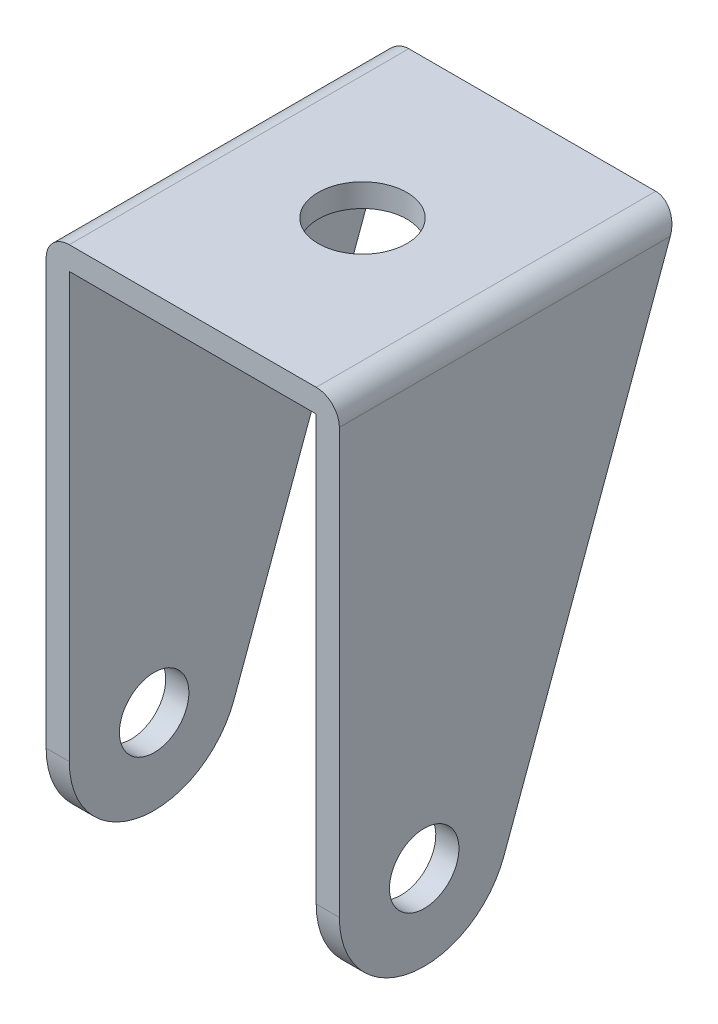
SolidWorks part; units mm, degrees
ref_plane "Front Plane" through (0, 0, 0) normal (0, 0, 1) x (1, 0, 0)
ref_plane "Top Plane" through (0, 0, 0) normal (0, 1, 0) x (1, 0, 0)
ref_plane "Right Plane" through (0, 0, 0) normal (1, 0, 0) x (0, 0, -1)
sketch "Sketch1" plane through (0, 0, 0) normal (1, 0, 0) x (0, 0, -1)
  line L0 (-11, 0) -> (-11, 58)
  line L1 (-11, 58) -> (33, 58)
  line L2 (33, 58) -> (10.3267, -3.7893)
  arc A0 (-11, 0) -> (10.3267, -3.7893) centre (0, 0) ccw
  dimension "D1" = 22
  dimension "D2" = 58
  dimension "D3" = 44
extrude "Boss-Extrude1" add sketch "Sketch1" along normal mid plane 38
sketch "Sketch2" plane through (0, 0, 11) normal (0, 0, 1) x (1, 0, 0)
  line L0 (-19, 58) -> (-19, 0) construction
  line L1 (-19, 58) -> (-19, 0)
  line L2 (19, 58) -> (-19, 58) construction
  line L3 (19, 58) -> (-19, 58)
  line L4 (19, 58) -> (19, 0) construction
  line L5 (19, 58) -> (19, 0)
  line L7 (19, -11) -> (19, 0) construction
  line L9 (19, -11) -> (19, 0)
  line L10 (-19, 0) -> (-19, -11) construction
  line L11 (-19, 0) -> (-19, -11)
  line L12 (16, -11) -> (16, 0)
  line L13 (16, 55) -> (16, 0)
  line L14 (16, 55) -> (-16, 55)
  line L15 (-16, 55) -> (-16, 0)
  line L16 (-16, 0) -> (-16, -11)
  line M4 (-19, 0) -> (19, 0)
  dimension "D1" = 3
extrude "Cut-Extrude1" cut sketch "Sketch2" against normal through all contours L14 L15 L13 M4
sketch "Sketch3" plane through (0, 0, 0) normal (0, 1, 0) x (1, 0, 0)
  line L4 (-16, 11.7172) -> (-16, -11)
  line L5 (-16, -11) -> (16, -11)
  line L6 (16, -11) -> (16, 11.7172)
  line L7 (16, 11.7172) -> (-16, 11.7172)
  line L8 (-16, 11.7172) -> (-16, -11)
  line L9 (-16, -11) -> (16, -11)
  line L10 (16, -11) -> (16, 11.7172)
  line L11 (16, 11.7172) -> (-16, 11.7172)
  dimension "D1" = 0
extrude "Cut-Extrude2" cut sketch "Sketch3" against normal through all
sketch "Sketch4" plane through (-19, 0, 0) normal (-1, 0, 0) x (0, 0, 1)
  circle A0 centre (0, 0) radius 4.5
  dimension "D1" = 9
extrude "Cut-Extrude3" cut sketch "Sketch4" against normal through all
sketch "Sketch5" plane through (0, 58, 0) normal (0, 1, 0) x (1, 0, 0)
  line L0 (19, -11) -> (-19, -11) construction
  circle A0 centre (0, 11) radius 5.75
  dimension "D1" = 11.5
  dimension "D2" = 22
extrude "Cut-Extrude4" cut sketch "Sketch5" against normal up to next
fillet "Fillet1" radius 3 2 edges at (19, 58, -11) (-19, 58, -11)
